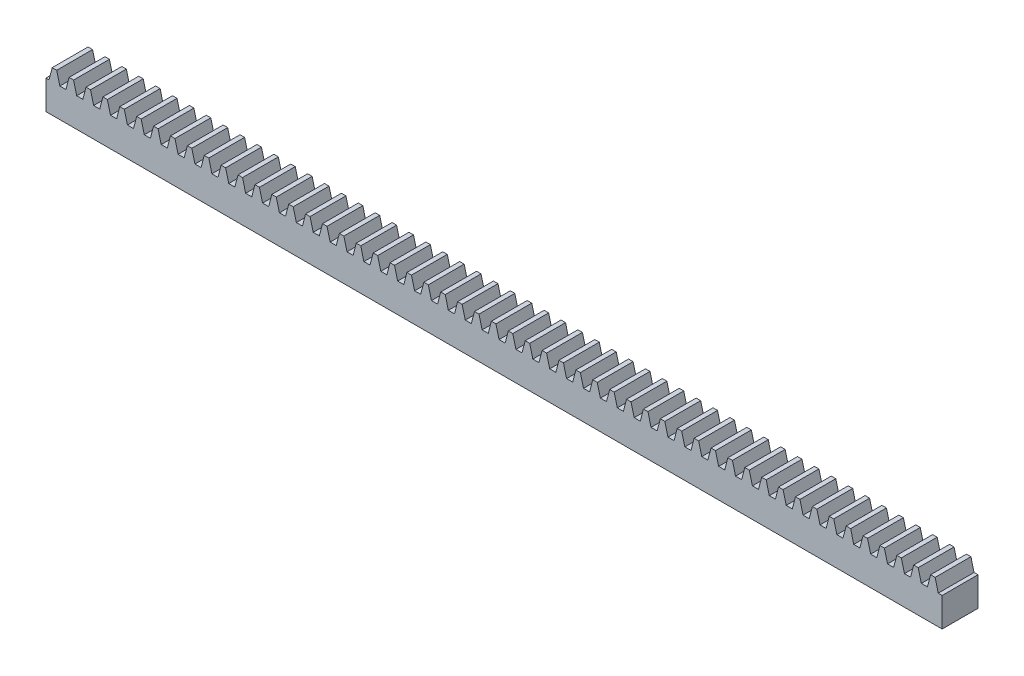
SolidWorks part; units mm, degrees
extrude "Blank" add sketch "BlankSke" against normal blind 10
sketch "BlankSke" plane through (0, 0, 0) normal (0, 0, 1) x (1, 0, 0)
  line L1 (0, 0) -> (250, 0)
  line L2 (0, 0) -> (0, 11.5)
  line L3 (0, 11.5) -> (250, 11.5)
  line L4 (250, 0) -> (250, 11.5)
  dimension "Length" = 250
  dimension "Blank_height" = 11.5
ref_plane "Plane1" through (0, 0, 0) normal (0, 0, 1) x (1, 0, 0)
ref_plane "Plane2" through (0, 0, 0) normal (0, 1, 0) x (1, 0, 0)
ref_plane "Plane3" through (0, 0, 0) normal (1, 0, 0) x (0, 0, -1)
sketch "HoldingSke" plane through (0, 0, 0) normal (0, 1, 0) x (1, 0, 0)
  line L0 (0, 0) -> (0.0928, 0.6602)
  line L1 (-15, 0) -> (100, 0) construction
  line L2 (0, 0) -> (-2.1039, 2.3779)
  line L3 (0, 0) -> (-11.863, 4.5341)
  line L4 (0, 0) -> (4.9534, 7.0742)
  line L5 (0, 0) -> (-23.7986, -8.8762)
  line L6 (0, 0) -> (-10.5278, -7.1032)
  line L9 (-67.7845, 28.3722) -> (174.2524, 90.9672)
  line L10 (-76.2, 3.8779) -> (-66.2, 3.8779)
  line L11 (0, 0) -> (-10, 0)
  line L12 (-76.2, 101.6) -> (-76.147, 101.6)
  line L13 (24.9733, 27.94) -> (52.9518, 28.4284)
  line L14 (24.9733, 27.94) -> (24.9743, 27.94)
  line L15 (24.9733, 27.94) -> (100.4006, 29.5858)
  circle A0 centre (0, 0) radius 19.05
  circle A1 centre (0, 0) radius 5
  circle A2 centre (0, 0) radius 12.7
  dimension "MPH" = 10
  dimension "Diameter" = 38.1
  dimension "Num_teeth" = 55
  dimension "Pitch" = 0.6667
  dimension "Show_teeth" = 998
  dimension "Thickness" = 12.7
  dimension "Ap" = 14.5
  dimension "Pitch_height" = 10
  dimension "Width" = 10
  dimension "Backlash" = 0.053
  dimension "Addendum_fac" = 1
  dimension "Dedendum_fac" = 1.25
  dimension "Clearance_fac" = 0.25
  dimension "Dedendum_add" = 0.001
  dimension "Length" = 250
  dimension "Module" = 1.5
sketch "TooCutSkeIll" plane through (0, 0, 0) normal (0, 0, 1) x (1, 0, 0)
  line L0 (-1.7134, 11.455) -> (-0.9251, 8.4069)
  line L1 (-0.5611, 8.125) -> (0.5611, 8.125)
  line L2 (0.9251, 8.4069) -> (1.7134, 11.455)
  line L3 (250, 11.5) -> (0, 11.5) construction
  line L4 (0, 0) -> (0, 64.897) construction
  line L5 (-13.208, 10) -> (12.954, 10) construction
  line L6 (0, 0) -> (250, 0) construction
  line L7 (1.3371, 10) -> (1.3371, 48.7463) construction
  line L8 (-1.3371, 10) -> (-1.3371, 48.7463) construction
  line L9 (1.7715, 11.5) -> (1.7715, 11.5254)
  line L10 (-1.7715, 11.5) -> (-1.7715, 11.5254)
  line L11 (-1.7715, 11.5254) -> (1.7715, 11.5254)
  arc A0 (0.5611, 8.125) -> (0.9251, 8.4069) centre (0.5611, 8.501) ccw
  arc A1 (-0.9251, 8.4069) -> (-0.5611, 8.125) centre (-0.5611, 8.501) ccw
  arc A2 (1.7715, 11.5) -> (1.7134, 11.455) centre (1.7715, 11.44) ccw
  arc A3 (-1.7134, 11.455) -> (-1.7715, 11.5) centre (-1.7715, 11.44) ccw
  dimension "Pitch_height" = 10
  dimension "Addendum_plus" = 1.5254
  dimension "Pressure_angle" = 14.5
  dimension "Gap_width" = 2.6742
  dimension "Dedendum" = 1.875
extrude "ToothCutIll" [suppressed] cut sketch "TooCutSkeIll" against normal through all
sketch "TooCutSkeSim" plane through (0, 0, 0) normal (0, 0, 1) x (1, 0, 0)
  line L0 (0.8522, 8.125) -> (-0.8522, 8.125)
  line L1 (1.7316, 11.5254) -> (0.8522, 8.125)
  line L2 (0, 17.4625) -> (0, 53.467) construction
  line L3 (1.7316, 11.5254) -> (-1.7316, 11.5254)
  line L6 (-1.7316, 11.5254) -> (-0.8522, 8.125)
  line L9 (-1.3371, 10) -> (1.3371, 10) construction
  line L10 (0, 0) -> (250, 0) construction
  line L11 (1.3371, 10) -> (1.3371, 53.467) construction
  line L12 (-1.3371, 10) -> (-1.3371, 53.467) construction
  dimension "Pitch_height" = 10
  dimension "Addendum_plus" = 1.5254
  dimension "Pressure_angle" = 14.5
  dimension "Gap_width" = 2.6742
  dimension "Dedendum" = 1.875
extrude "ToothCutSim" cut sketch "TooCutSkeSim" against normal through all
pattern_linear "TeethCuts" count 54 spacing 4.7124 along (1, 0, 0) of "ToothCutIll", "ToothCutSim"
equation "' \"Module@HoldingSke\" = 6.35"
equation "' \"Num_teeth@HoldingSke\" = 12"
equation "' \"Ap@HoldingSke\" =  20"
equation "' \"Ap@HoldingSke\" = 20"
equation "' \"Width@HoldingSke\" = 0.25 * 25.4"
equation "' \"Show_teeth@HoldingSke\" = 500"
equation "' \"Backlash@HoldingSke\" = 0.009 * 25.4"
equation "' \"Addendum_fac@HoldingSke\" = 1.0"
equation "' \"Dedendum_fac@HoldingSke\" = 1.25"
equation "' \"Dedendum_add@HoldingSke\" = 0.00005 * 25.4"
equation "' \"Clearance_fac@HoldingSke\" = 0.25"
equation "' \"Pitch_height@HoldingSke\" = 1 * 25.4"
equation "' \"Length@HoldingSke\" = 4.71 * 25.4"
equation "\"Pitch@HoldingSke\" = 1 / \"Module@HoldingSke\""
equation "\"MPH@HoldingSke\" = \"Dedendum_fac@HoldingSke\" / \"Pitch@HoldingSke\" + 2 * \"Dedendum_add@HoldingSke\" + 0.002 * 25.4"
equation "\"MPH@HoldingSke\" = ((sgn( \"MPH@HoldingSke\" - \"Pitch_height@HoldingSke\")+1)*( \"MPH@HoldingSke\" - \"Pitch_height@HoldingSke\"))/2 + \"Pitch_height@HoldingSke\""
equation "\"Blank_height@BlankSke\" = \"Pitch_height@HoldingSke\" + \"Addendum_fac@HoldingSke\"  / \"Pitch@HoldingSke\" "
equation "\"Length@BlankSke\" =  \"Length@HoldingSke\""
equation "\"Face_width@Blank\" = \"Width@HoldingSke\""
equation "\"Pressure_angle@TooCutSkeIll\" = \"Ap@HoldingSke\""
equation "\"Addendum_plus@TooCutSkeIll\" =  \"Addendum_fac@HoldingSke\"  / \"Pitch@HoldingSke\" + 0.001 *25.4"
equation "\"Dedendum@TooCutSkeIll\" = \"Dedendum_fac@HoldingSke\"  / \"Pitch@HoldingSke\""
equation "\"Pitch_height@TooCutSkeIll\" =  \"MPH@HoldingSke\""
equation "\"Gap_width@TooCutSkeIll\" = 3.14159265 / 2 / \"Pitch@HoldingSke\" + 6 * \"Backlash@HoldingSke\""
equation "\"Pressure_angle@TooCutSkeSim\" = \"Ap@HoldingSke\""
equation "\"Addendum_plus@TooCutSkeSim\" =  \"Addendum_fac@HoldingSke\"  / \"Pitch@HoldingSke\" + 0.001 * 25.4"
equation "\"Dedendum@TooCutSkeSim\" = \"Dedendum_fac@HoldingSke\"  / \"Pitch@HoldingSke\""
equation "\"Pitch_height@TooCutSkeSim\" =  \"MPH@HoldingSke\""
equation "\"Gap_width@TooCutSkeSim\" = 3.14159265 / 2 / \"Pitch@HoldingSke\" + 6 * \"Backlash@HoldingSke\""
equation "\"Root_fillet@TooCutSkeIll\" = \"Clearance_fac@HoldingSke\" / \"Pitch@HoldingSke\" + \"Dedendum_add@HoldingSke\""
equation "\"Break_rad@TooCutSkeIll\" = 0.02 / \"Pitch@HoldingSke\" * 2"
equation "\"Linear_pitch@TeethCuts\" = 3.14159265 / \"Pitch@HoldingSke\""
equation "\"Num_teeth@HoldingSke\" = int( ( \"Length@HoldingSke\" + 0 ) / (3.14159265 / \"Pitch@HoldingSke\")) + 0.9999  + 1"
equation " \"Num_teeth@TeethCuts\" = int( \"Show_teeth@HoldingSke\" ) + 1"
equation " \"Num_teeth@TeethCuts\" = ((sgn( \"Num_teeth@TeethCuts\" - \"Num_teeth@HoldingSke\" )-1)*( \"Num_teeth@TeethCuts\" - \"Num_teeth@HoldingSke\" ))/-2+ \"Num_teeth@HoldingSke\""
equation " \"Num_teeth@TeethCuts\" = ((sgn( \"Num_teeth@TeethCuts\" - 2.0)+1)*( \"Num_teeth@TeethCuts\" - 2.0))/2 +2.0"
